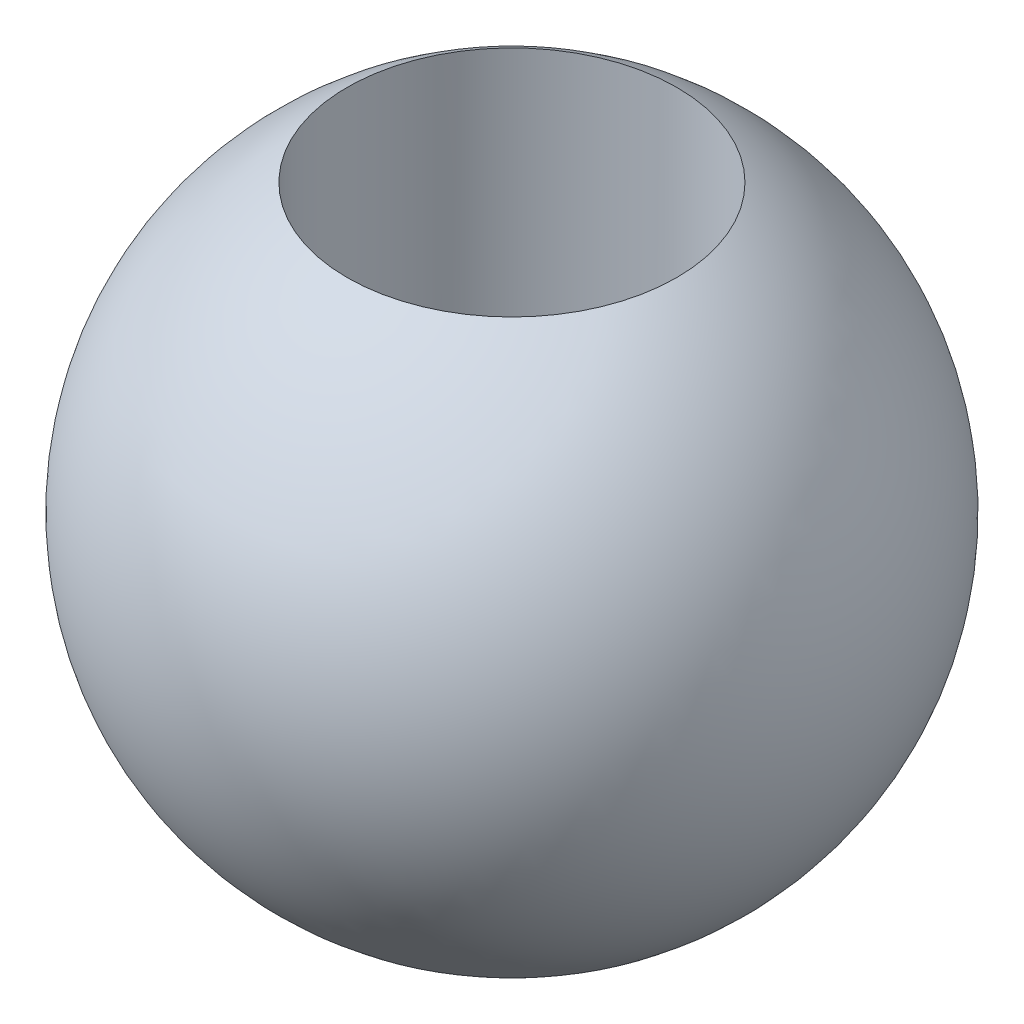
SolidWorks part; units mm, degrees
material "Cast Alloy Steel"
ref_plane "Front Plane" through (0, 0, 0) normal (0, 0, 1) x (1, 0, 0)
ref_plane "Top Plane" through (0, 0, 0) normal (0, 1, 0) x (1, 0, 0)
ref_plane "Right Plane" through (0, 0, 0) normal (1, 0, 0) x (0, 0, -1)
sketch "Sketch1" plane through (0, 0, 0) normal (0, 0, 1) x (1, 0, 0)
  line L0 (0, 10) -> (0, -10) construction
  line L1 (0, -10) -> (0, 10)
  arc A0 (0, -10) -> (0, 10) centre (0, 0) ccw
  arc A1 (0, 10) -> (0, -10) centre (0, 0) ccw construction
  point P5 (0, -10)
  dimension "D1" = 20
revolve "Revolve2" add sketch "Sketch1" angle 360 about L0
ref_plane "Plane1" through (0, 10, 0) normal (0, 1, 0) x (1, 0, 0)
sketch "Sketch4" plane through (0, 10, 0) normal (0, 1, 0) x (1, 0, 0)
  circle A0 centre (0, 0) radius 5
  point P0 (0, 0)
  dimension "D1" = 10
extrude "Cut-Extrude1" cut sketch "Sketch4" against normal blind 12.5
